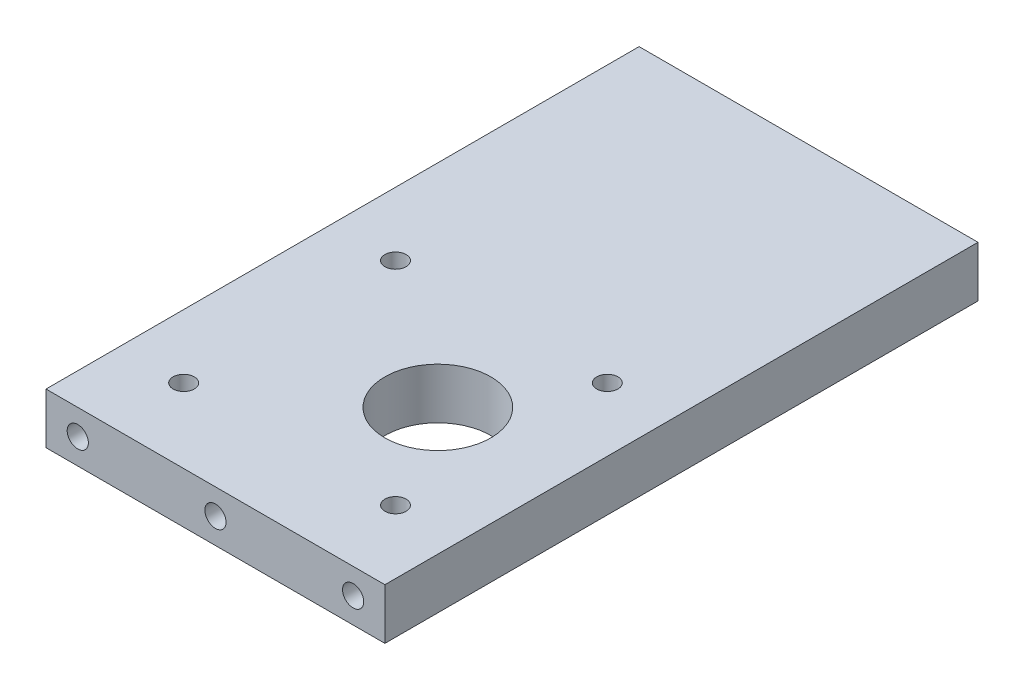
SolidWorks part; units mm, degrees
ref_plane "Front Plane" through (0, 0, 0) normal (0, 0, 1) x (1, 0, 0)
ref_plane "Top Plane" through (0, 0, 0) normal (0, 1, 0) x (1, 0, 0)
ref_plane "Right Plane" through (0, 0, 0) normal (1, 0, 0) x (0, 0, -1)
sketch "Sketch1" plane through (0, 0, 0) normal (0, 1, 0) x (1, 0, 0)
  line L0 (0, 0) -> (0, 140.817) construction
  line L1 (-40, 140) -> (40, 140)
  line L2 (-40, 140) -> (-40, 0)
  line L3 (-40, 0) -> (40, 0)
  line L4 (40, 140) -> (40, 0)
  circle A0 centre (10, 42.5) radius 12.5
  dimension "D4" = 25
  dimension "D1" = 80
  dimension "D2" = 140
  dimension "D3" = 97.5
  dimension "D5" = 30
extrude "Boss-Extrude1" add sketch "Sketch1" along normal mid plane 12
sketch "Sketch2" plane through (0, 6, 0) normal (0, 1, 0) x (1, 0, 0)
  line L0 (54.8315, 42.5) -> (-86.9211, 42.5) construction
  line L1 (0, 0) -> (0, 153.7848) construction
  line L2 (-40, 0) -> (40, 0) construction
  point P0 (25, 67.5)
  point P1 (-25, 67.5)
  point P2 (-25, 17.5)
  point P3 (25, 17.5)
  point P14 (10, 42.5)
  dimension "D1" = 50
  dimension "D3" = 50
hole_wizard "Tap Drill for M6 Tap1" positions "Sketch3" profile "Sketch5" hole size "M6" standard "ISO" end condition through all
sketch "Sketch3" plane through (0, 6, 0) normal (0, 1, 0) x (1, 0, 0)
  point P0 (-25, 67.5)
  point P3 (25, 67.5)
  point P6 (25, 17.5)
  point P9 (-25, 17.5)
sketch "Sketch5" plane through (-25, 6, -67.5) normal (1, 0, 0) x (0, 0, 1)
  line L0 (0, 0) -> (0, 12)
  line L1 (0, 12) -> (2.5, 12)
  line L2 (2.5, 12) -> (2.5, 0)
  line L5 (2.5, 0) -> (0, 0)
  line L11 (0, -6.35) -> (0, 107.95) construction
  dimension "Thru Hole Dia." = 5
  dimension "Thru Hole Depth" = 12
sketch "Sketch7" plane through (0, 0, 0) normal (0, 0, 1) x (1, 0, 0)
  line L0 (34.4527, 0) -> (-37.6381, 0) construction
  line L3 (0, 12.2814) -> (0, -18.3619) construction
  point P3 (32.5, 0)
  point P4 (0, 0)
  point P6 (-32.5, 0)
  dimension "D1" = 65
hole_wizard "Tap Drill for M6 Tap2" positions "Sketch8" profile "Sketch9" hole size "M6" standard "ISO"
sketch "Sketch8" plane through (0, 0, 0) normal (0, 0, 1) x (1, 0, 0)
  point P0 (32.5, 0)
  point P3 (0, 0)
  point P6 (-32.5, 0)
sketch "Sketch9" plane through (32.5, 0, 0) normal (1, 0, 0) x (0, -1, 0)
  line L0 (0, 0) -> (0, 21.5022)
  line L1 (0, 21.5022) -> (2.5, 20)
  line L2 (2.5, 20) -> (2.5, 0)
  line L5 (2.5, 0) -> (0, 0)
  line L10 (0, 21.5022) -> (-2.5, 20) construction
  line L11 (0, -6.35) -> (0, 107.95) construction
  dimension "Hole Dia." = 5
  dimension "Hole Depth" = 20
  dimension "Drill Angle" = 118
ref_plane "Plane1" through (0, 0, -70) normal (0, 0, -1) x (-1, 0, 0)
mirror "Mirror1" about plane through (0, 0, -70) normal (0, 0, -1) of "Tap Drill for M6 Tap2"
sketch "Sketch10" plane through (-40, 0, 0) normal (-1, 0, 0) x (0, 0, 1)
  line L0 (0, 0) -> (-142.6132, 0) construction
  line L1 (-140, 6) -> (-140, -6) construction
  point P0 (-113, 0)
  point P1 (-86, 0)
  point P2 (-56, 0)
  point P6 (-29, 0)
  dimension "D1" = 27
  dimension "D2" = 27
  dimension "D3" = 30
  dimension "D4" = 27
hole_wizard "Tap Drill for M6 Tap3" positions "Sketch11" profile "Sketch12" hole size "M6" standard "ISO"
sketch "Sketch11" plane through (-40, 0, 0) normal (-1, 0, 0) x (0, 0, 1)
  point P0 (-113, 0)
  point P3 (-86, 0)
  point P6 (-56, 0)
  point P9 (-29, 0)
sketch "Sketch12" plane through (-40, 0, -113) normal (0, 1, 0) x (0, 0, 1)
  line L0 (0, 0) -> (0, 27.5022)
  line L1 (0, 27.5022) -> (2.5, 26)
  line L2 (2.5, 26) -> (2.5, 0)
  line L5 (2.5, 0) -> (0, 0)
  line L10 (0, 27.5022) -> (-2.5, 26) construction
  line L11 (0, -6.35) -> (0, 107.95) construction
  dimension "Hole Dia." = 5
  dimension "Hole Depth" = 26
  dimension "Drill Angle" = 118
